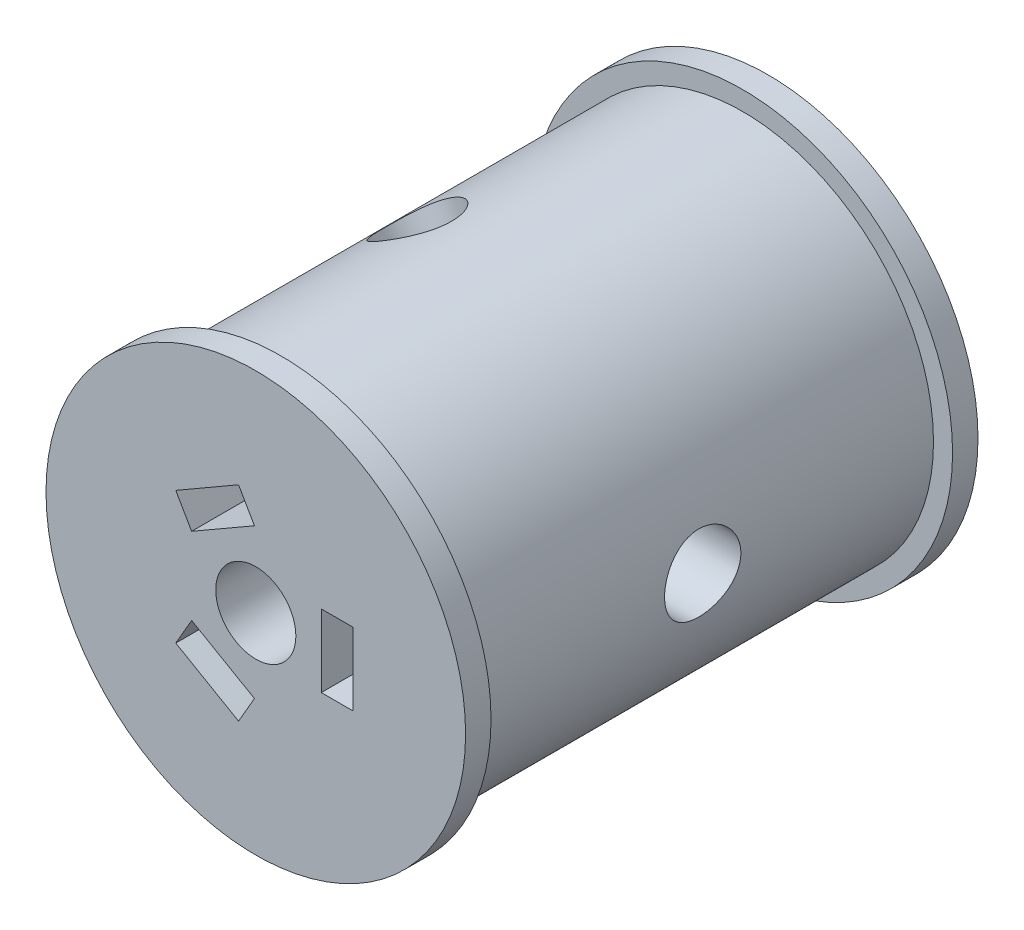
SolidWorks part; units mm, degrees
ref_plane "Front" through (0, 0, 0) normal (0, 0, 1) x (1, 0, 0)
ref_plane "Top" through (0, 0, 0) normal (0, 1, 0) x (1, 0, 0)
ref_plane "Right" through (0, 0, 0) normal (1, 0, 0) x (0, 0, -1)
sketch "Sketch1" plane through (0, 0, 0) normal (0, 0, 1) x (1, 0, 0)
  circle A0 centre (0, 0) radius 15
  circle A1 centre (0, 0) radius 3.15
  dimension "D1" = 30
  dimension "D2" = 6.3
extrude "Boss-Extrude1" add sketch "Sketch1" along normal blind 40.3
sketch "Sketch2" plane through (0, 0, 40.3) normal (0, 0, 1) x (1, 0, 0)
  line L3 (7.65, 0) -> (7.65, 2.85)
  line L5 (7.65, 0) -> (7.65, -2.85)
  line L7 (7.65, 2.85) -> (5.15, 2.85)
  line L8 (5.15, 2.85) -> (5.15, -2.85)
  line L9 (5.15, -2.85) -> (7.65, -2.85)
  line L16 (-3.825, -6.6251) -> (-1.3568, -8.0501)
  line L17 (-3.825, -6.6251) -> (-6.2932, -5.2001)
  line L18 (-1.3568, -8.0501) -> (-0.1068, -5.885)
  line L19 (-0.1068, -5.885) -> (-5.0432, -3.035)
  line L20 (-5.0432, -3.035) -> (-6.2932, -5.2001)
  line L21 (-3.825, 6.6251) -> (-6.2932, 5.2001)
  line L22 (-3.825, 6.6251) -> (-1.3568, 8.0501)
  line L23 (-1.3568, 8.0501) -> (-0.1054, 5.8826)
  line L24 (-0.1054, 5.8826) -> (-5.0482, 3.0353)
  line L25 (-5.0482, 3.0353) -> (-6.2932, 5.2001)
  dimension "D5" = 2.85
  dimension "D6" = 2.85
  dimension "D7" = 2.85
  dimension "D8" = 2.85
  dimension "D9" = 2.5
  dimension "D10" = 5.7
  dimension "D11" = 2.85
extrude "Cut-Extrude1" cut sketch "Sketch2" against normal blind 23 contours L9 L5 L3 L7 L8 | L25 L21 L22 L23 L24 | L20 L17 L16 L18 L19
ref_plane "Plane1" through (-7.5, -12.9904, 0) normal (-0.5, -0.866, 0) x (0, 0, -1)
sketch "Sketch8" plane through (-7.5, -12.9904, 0) normal (-0.5, -0.866, 0) x (0, 0, -1)
  circle A0 centre (-20.15, 0) radius 1.65
  dimension "D1" = 3.3
extrude "Cut-Extrude4" cut sketch "Sketch8" against normal up to next
sketch "Sketch10" plane through (-7.5, -12.9904, 0) normal (-0.5, -0.866, 0) x (0, 0, -1)
  circle A0 centre (-20.15, 0) radius 1.65
extrude "Cut-Extrude5" cut sketch "Sketch10" against normal up to next
sketch "Sketch12" plane through (-7.5, -12.9904, 0) normal (-0.5, -0.866, 0) x (0, 0, -1)
  circle A0 centre (-20.15, 0) radius 3
  dimension "D1" = 6
extrude "Cut-Extrude6" cut sketch "Sketch12" against normal blind 5.35
ref_plane "Plane2" through (-7.5, 12.9904, 0) normal (-0.5, 0.866, 0) x (0, 0, -1)
sketch "Sketch15" plane through (-7.5, 12.9904, 0) normal (-0.5, 0.866, 0) x (0, 0, -1)
  circle A0 centre (-20.15, 0) radius 3
extrude "Cut-Extrude8" cut sketch "Sketch15" against normal blind 5.35
sketch "Sketch17" plane through (-7.5, 12.9904, 0) normal (-0.5, 0.866, 0) x (0, 0, -1)
  circle A0 centre (-20.15, 0) radius 1.65
  dimension "D1" = 3.3
extrude "Cut-Extrude9" cut sketch "Sketch17" against normal up to next
sketch "Sketch18" plane through (-7.5, 12.9904, 0) normal (-0.5, 0.866, 0) x (0, 0, -1)
  circle A0 centre (-20.15, 0) radius 1.65
extrude "Cut-Extrude10" cut sketch "Sketch18" against normal up to next
ref_plane "Plane3" through (15, 0, 0) normal (1, 0, 0) x (0, 0, -1)
sketch "Sketch19" plane through (15, 0, 0) normal (1, 0, 0) x (0, 0, -1)
  circle A0 centre (-20.15, 0) radius 3
extrude "Cut-Extrude11" cut sketch "Sketch19" against normal blind 5.35 contours A0
sketch "Sketch20" plane through (15, 0, 0) normal (1, 0, 0) x (0, 0, -1)
  circle A0 centre (-20.15, 0) radius 1.65
  dimension "D1" = 3.3
extrude "Cut-Extrude12" cut sketch "Sketch20" against normal up to next
sketch "Sketch21" plane through (15, 0, 0) normal (1, 0, 0) x (0, 0, -1)
  circle A0 centre (-20.15, 0) radius 1.65
extrude "Cut-Extrude13" cut sketch "Sketch21" against normal up to next
sketch "Sketch22" plane through (0, 0, 40.3) normal (0, 0, 1) x (1, 0, 0)
  line L0 (-1.3568, -8.0501) -> (-0.1068, -5.885)
  line L1 (7.65, -2.85) -> (5.15, -2.85)
  line L2 (7.65, -2.85) -> (7.65, 2.85)
  line L3 (7.65, 2.85) -> (5.15, 2.85)
  line L4 (5.15, -2.85) -> (5.15, 2.85)
  line L5 (-0.1068, -5.885) -> (-5.0432, -3.035)
  line L6 (-5.0432, -3.035) -> (-6.2932, -5.2001)
  line L7 (-1.3568, -8.0501) -> (-6.2932, -5.2001) construction
  line L8 (-5.0432, -3.035) -> (-6.2932, -5.2001) construction
  line L9 (-6.2932, -5.2001) -> (-1.3568, -8.0501)
  line L10 (-5.0482, 3.0353) -> (-0.1054, 5.8826)
  line L11 (-0.1054, 5.8826) -> (-1.3568, 8.0501)
  line L12 (-1.3568, 8.0501) -> (-6.2932, 5.2001)
  line L13 (-6.2932, 5.2001) -> (-1.3568, 8.0501) construction
  line L14 (-5.0482, 3.0353) -> (-6.2932, 5.2001) construction
  line L15 (-6.2932, 5.2001) -> (-5.0482, 3.0353)
  circle A0 centre (0, 0) radius 16.5
  circle A1 centre (0, 0) radius 3.15
  dimension "D1" = 33
extrude "Boss-Extrude3" add sketch "Sketch22" against normal blind 2
sketch "Sketch23" plane through (0, 0, 0) normal (0, 0, -1) x (-1, 0, 0)
  circle A0 centre (0, 0) radius 16.5
  circle A1 centre (0, 0) radius 3.15
  dimension "D1" = 33
extrude "Boss-Extrude4" add sketch "Sketch23" against normal blind 2
